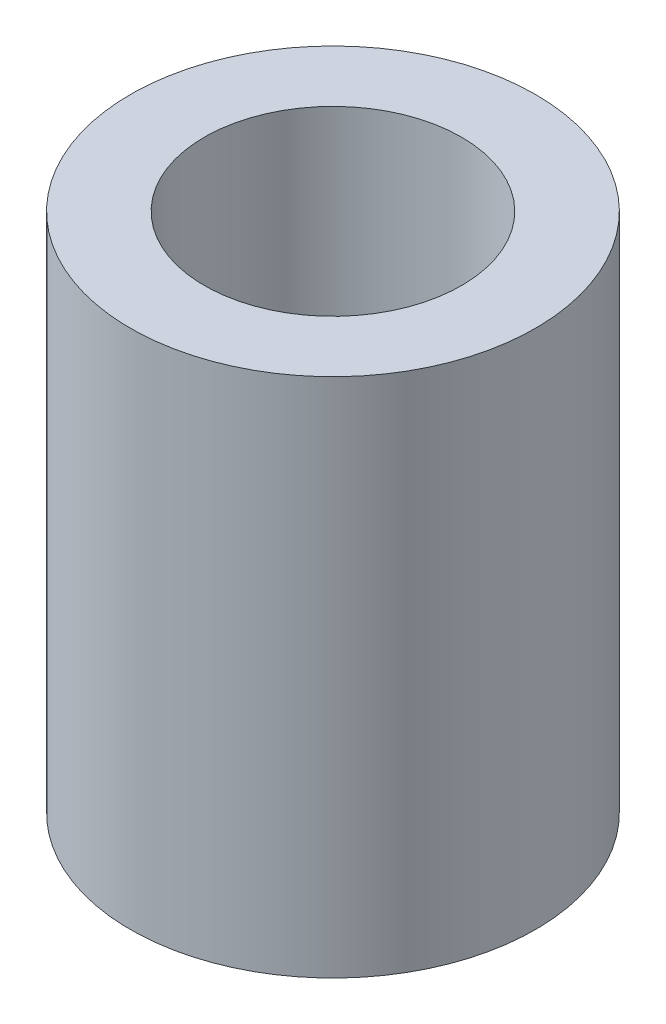
SolidWorks part; units mm, degrees
material "Brass"
ref_plane "Front Plane" through (0, 0, 0) normal (0, 0, 1) x (1, 0, 0)
ref_plane "Top Plane" through (0, 0, 0) normal (0, 1, 0) x (1, 0, 0)
ref_plane "Right Plane" through (0, 0, 0) normal (1, 0, 0) x (0, 0, -1)
sketch "Sketch1" plane through (0, 0, 0) normal (0, 0, 1) x (1, 0, 0)
  line L0 (0, 0) -> (0, 8.1) construction
  line L2 (2, 8.1) -> (2, 0)
  line L4 (2, 8.1) -> (3.15, 8.1)
  line L5 (3.15, 8.1) -> (3.15, 0)
  line L7 (3.15, 0) -> (2, 0)
  dimension "D1" = 8.1
  dimension "D2" = 2
  dimension "D3" = 3.15
revolve "Revolve1" add sketch "Sketch1" angle 360 about L0
